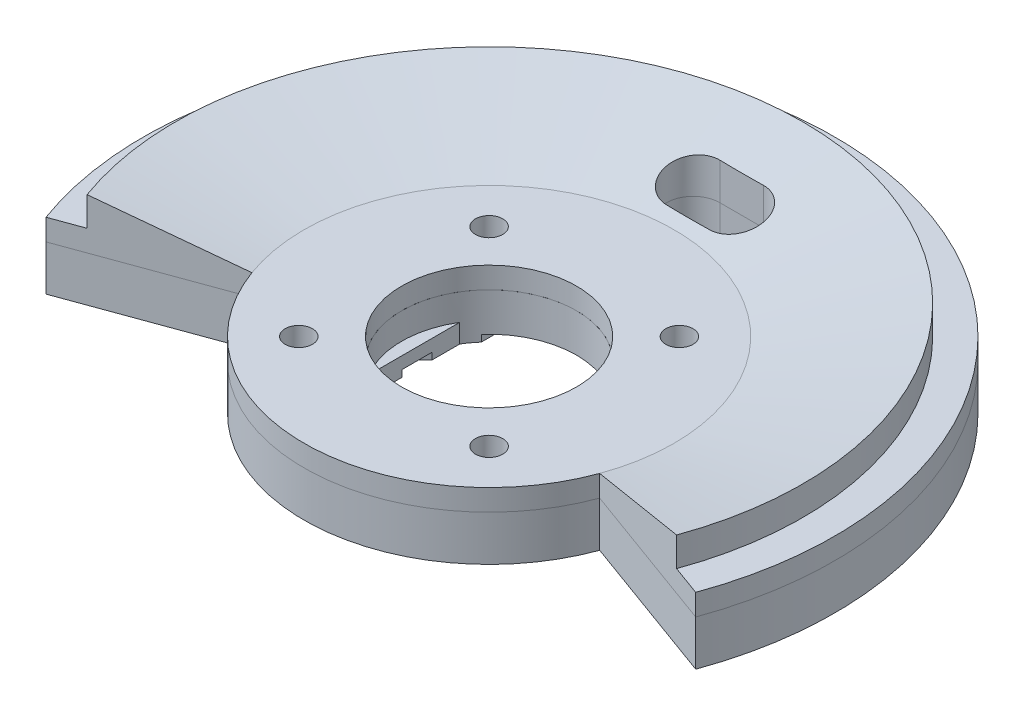
SolidWorks part; units mm, degrees
ref_plane "Front Plane" through (0, 0, 0) normal (0, 0, 1) x (1, 0, 0)
ref_plane "Top Plane" through (0, 0, 0) normal (0, 1, 0) x (1, 0, 0)
ref_plane "Right Plane" through (0, 0, 0) normal (1, 0, 0) x (0, 0, -1)
sketch "Sketch2" plane through (0, 0, 0) normal (0, 1, 0) x (1, 0, 0)
  circle A1 centre (-14.1421, 14.1421) radius 1.65 construction
  circle A2 centre (14.1421, 14.1421) radius 1.65 construction
  circle A3 centre (14.1421, -14.1421) radius 1.65 construction
  circle A4 centre (-14.1421, -14.1421) radius 1.65 construction
  circle A5 centre (0, 0) radius 13
  circle A6 centre (-14.1421, 14.1421) radius 1.65 construction
  circle A7 centre (14.1421, 14.1421) radius 1.65 construction
  circle A8 centre (14.1421, -14.1421) radius 1.65 construction
  circle A9 centre (-14.1421, -14.1421) radius 1.65 construction
  arc A10 (10.7886, -7.253) -> (10.7886, 7.253) centre (0, 0) ccw construction
  circle A11 centre (0, 0) radius 27.5
  circle A12 centre (0, 0) radius 27.5 construction
  circle A13 centre (-14.1421, -14.1421) radius 2.025
  circle A14 centre (14.1421, -14.1421) radius 2.025
  circle A15 centre (14.1421, 14.1421) radius 2.025
  circle A16 centre (-14.1421, 14.1421) radius 2.025
  dimension "D1" = 4.05
extrude "Boss-Extrude1" add sketch "Sketch2" against normal blind 3.175 from surface at -14.125
sketch "Sketch3" plane through (0, 0, 0) normal (0, 1, 0) x (1, 0, 0)
  circle A0 centre (0, 0) radius 12
  circle A1 centre (0, 0) radius 12 construction
  circle A2 centre (0, 0) radius 18.35
  dimension "D1" = 6.35
extrude "Boss-Extrude2" add sketch "Sketch3" along normal blind 6 from surface separate body
sketch "Sketch4" plane through (0, 0, 0) normal (1, 0, 0) x (0, 0, -1)
  line L0 (27.5, -17.3) -> (51.3863, -17.3)
  line L1 (51.3863, -17.3) -> (51.3863, 34.4275)
  line L2 (27.5, -14.125) -> (46.6238, -9.7953)
  line L3 (36.33, -12.1258) -> (45.83, -9.975) construction
  line L4 (45.83, -9.975) -> (45.83, 5.525) construction
  line L5 (46.6238, -9.7953) -> (46.6238, 28.4275)
  line L7 (46.6238, 28.4275) -> (18.35, 28.4275)
  line L9 (51.3863, 34.4275) -> (18.35, 34.4275)
  line L10 (18.35, 34.4275) -> (18.35, 28.4275)
  line L16 (0, -14.125) -> (0, 28.4275) construction
  line L17 (13, -14.125) -> (-13, -14.125) construction
  line L18 (-18.35, 28.4275) -> (18.35, 28.4275) construction
  line L19 (27.5, -17.3) -> (27.5, -14.125)
  dimension "D1" = 0.7937
  dimension "D2" = 4.7625
revolve "Revolve1" add sketch "Sketch4" angle 220 mid plane about L16
sketch "Sketch5" plane through (0, 28.4275, 0) normal (0, -1, 0) x (1, 0, 0)
  circle A0 centre (0, 0) radius 11.2063
  circle A1 centre (0, 0) radius 18.35
  arc A2 (17.2434, 6.2761) -> (-17.2434, 6.2761) centre (0, 0) ccw construction
  circle A3 centre (0, 0) radius 12 construction
  dimension "D1" = 0.7937
extrude "Boss-Extrude3" add sketch "Sketch5" along normal blind 0.7937
fillet "Fillet1" [suppressed] radius 1.5875
sketch "Sketch6" plane through (0, -17.3, 0) normal (0, -1, 0) x (-1, 0, 0)
  line L0 (3.25, 33.58) -> (-3.25, 33.58) construction
  line L1 (3.25, 29.6113) -> (-3.25, 29.6113)
  line L2 (3.25, 37.5488) -> (-3.25, 37.5488)
  arc A0 (3.25, 29.6113) -> (3.25, 37.5488) centre (3.25, 33.58) ccw
  arc A1 (-3.25, 37.5488) -> (-3.25, 29.6113) centre (-3.25, 33.58) ccw
  point P4 (0, 33.58)
  dimension "D1" = 7.9375
extrude "Cut-Extrude1" cut sketch "Sketch6" against normal up to next
sketch "Sketch7" plane through (0, 34.4275, 0) normal (0, 1, 0) x (1, 0, 0)
  line L0 (-48.2873, -17.5751) -> (-43.812, -15.9463)
  line L1 (43.812, -15.9463) -> (48.2873, -17.5751)
  arc A0 (48.2873, -17.5751) -> (-48.2873, -17.5751) centre (0, 0) ccw construction
  arc A1 (43.812, -15.9463) -> (-43.812, -15.9463) centre (0, 0) ccw construction
  arc A2 (48.2873, -17.5751) -> (-48.2873, -17.5751) centre (0, 0) ccw
  arc A3 (43.812, -15.9463) -> (-43.812, -15.9463) centre (0, 0) ccw
extrude "Cut-Extrude2" cut sketch "Sketch7" against normal offset from surface (48.5525 mm away) 3.175 up to face at (0, -17.3, -33.58)
sketch "Sketch8" plane through (0, -17.3, 0) normal (0, -1, 0) x (1, 0, 0)
  line L2 (-3.25, -37.5488) -> (3.25, -37.5488)
  line L3 (3.25, -29.6113) -> (-3.25, -29.6113)
  line L4 (-3.25, -37.5488) -> (3.25, -37.5488)
  line L5 (3.25, -29.6113) -> (-3.25, -29.6113)
  line L6 (-25.8415, 9.4056) -> (-48.2873, 17.5751)
  line L7 (48.2873, 17.5751) -> (25.8415, 9.4056)
  line L8 (-25.8415, 9.4056) -> (-48.2873, 17.5751)
  line L9 (48.2873, 17.5751) -> (25.8415, 9.4056)
  circle A1 centre (-14.1421, -14.1421) radius 2.025
  arc A2 (3.25, -37.5488) -> (3.25, -29.6113) centre (3.25, -33.58) ccw
  arc A3 (-3.25, -29.6113) -> (-3.25, -37.5488) centre (-3.25, -33.58) ccw
  arc A4 (3.25, -37.5488) -> (3.25, -29.6113) centre (3.25, -33.58) ccw
  arc A5 (-3.25, -29.6113) -> (-3.25, -37.5488) centre (-3.25, -33.58) ccw
  circle A6 centre (-14.1421, -14.1421) radius 2.025
  circle A7 centre (14.1421, -14.1421) radius 2.025
  circle A8 centre (14.1421, -14.1421) radius 2.025
  circle A9 centre (14.1421, 14.1421) radius 2.025
  circle A10 centre (14.1421, 14.1421) radius 2.025
  circle A11 centre (-14.1421, 14.1421) radius 2.025
  circle A12 centre (-14.1421, 14.1421) radius 2.025
  circle A13 centre (0, 0) radius 13
  circle A14 centre (0, 0) radius 13
  arc A16 (25.8415, 9.4056) -> (-25.8415, 9.4056) centre (0, 0) ccw
  arc A17 (-48.2873, 17.5751) -> (48.2873, 17.5751) centre (0, 0) ccw
  arc A18 (25.8415, 9.4056) -> (-25.8415, 9.4056) centre (0, 0) ccw
  arc A19 (-48.2873, 17.5751) -> (48.2873, 17.5751) centre (0, 0) ccw
  dimension "D1" = 0
  dimension "D2" = 0
  dimension "D3" = 0
  dimension "D4" = 0
  dimension "D5" = 0
  dimension "D6" = 0
  dimension "D7" = 0
extrude "Boss-Extrude4" add sketch "Sketch8" along normal up to surface (6.7238 mm away) separate body
sketch "Sketch10" plane through (0, -24.0238, 0) normal (0, -1, 0) x (1, 0, 0)
  line L0 (-11.1125, 0) -> (11.1125, 0) construction
  line L1 (-11.1125, 6.7463) -> (-13, 6.7463)
  line L2 (-11.1125, 6.7463) -> (-11.1125, -6.7463)
  line L3 (-11.1125, -6.7463) -> (-13, -6.7463)
  line L4 (-13, 6.7463) -> (-13, -6.7463)
  line L5 (13, 6.7463) -> (11.1125, 6.7463)
  line L6 (13, 6.7463) -> (13, -6.7463)
  line L7 (13, -6.7463) -> (11.1125, -6.7463)
  line L8 (11.1125, 6.7463) -> (11.1125, -6.7463)
  circle A0 centre (0, 0) radius 13 construction
  point P12 (0, 0)
  dimension "D1" = 22.225
ref_plane "Plane1" through (-10.7886, -14.125, -7.253) normal (-0.5579, 0, 0.8299) x (0.8299, 0, 0.5579)
ref_plane "Plane2" through (-10.7886, -14.125, -7.253) normal (-0.5579, 0, 0.8299) x (0.8299, 0, 0.5579)
extrude "Boss-Extrude5" add sketch "Sketch10" against normal offset from surface (2.7938 mm away) 1.5875
sketch "Sketch12" plane through (0, -24.0238, 0) normal (0, -1, 0) x (1, 0, 0)
  line L0 (-9.754, -3.9818) -> (-9.754, -20.6306)
  line L1 (-9.754, -20.6306) -> (9.754, -20.6306)
  line L6 (9.754, -20.6306) -> (9.754, -3.9818)
  line L7 (9.754, -3.9818) -> (12.754, -0.9818)
  line L8 (12.754, -0.9818) -> (12.754, 0.2286)
  line L9 (12.754, 0.2286) -> (9.754, 3.2286)
  line L10 (9.754, 3.2286) -> (9.754, 4.8774)
  line L11 (9.754, 4.8774) -> (-9.754, 4.8774)
  line L12 (-9.754, 4.8774) -> (-9.754, 3.2286)
  line L13 (-9.754, 3.2286) -> (-12.754, 0.2286)
  line L14 (-12.754, 0.2286) -> (-12.754, -0.9818)
  line L15 (-12.754, -0.9818) -> (-9.754, -3.9818)
  line L16 (-9.5, -3.8766) -> (-9.5, -20.3766)
  line L17 (-9.5, -20.3766) -> (9.5, -20.3766)
  line L18 (9.5, -20.3766) -> (9.5, -3.8766)
  line L19 (9.5, -3.8766) -> (12.5, -0.8766)
  line L20 (12.5, -0.8766) -> (12.5, 0.1234)
  line L21 (12.5, 0.1234) -> (9.5, 3.1234)
  line L22 (9.5, 3.1234) -> (9.5, 4.6234)
  line L23 (9.5, 4.6234) -> (-9.5, 4.6234)
  line L24 (-9.5, 4.6234) -> (-9.5, 3.1234)
  line L25 (-9.5, 3.1234) -> (-12.5, 0.1234)
  line L26 (-12.5, 0.1234) -> (-12.5, -0.8766)
  line L27 (-12.5, -0.8766) -> (-9.5, -3.8766)
  line L28 (-9.5, -3.8766) -> (-9.5, -20.3766) construction
  line L29 (-9.5, -20.3766) -> (9.5, -20.3766) construction
  line L30 (9.5, -20.3766) -> (9.5, -3.8766) construction
  line L31 (9.5, -3.8766) -> (12.5, -0.8766) construction
  line L32 (12.5, -0.8766) -> (12.5, 0.1234) construction
  line L33 (12.5, 0.1234) -> (9.5, 3.1234) construction
  line L34 (9.5, 3.1234) -> (9.5, 4.6234) construction
  line L35 (9.5, 4.6234) -> (-9.5, 4.6234) construction
  line L36 (-9.5, 4.6234) -> (-9.5, 3.1234) construction
  line L37 (-9.5, 3.1234) -> (-12.5, 0.1234) construction
  line L38 (-12.5, 0.1234) -> (-12.5, -0.8766) construction
  line L39 (-12.5, -0.8766) -> (-9.5, -3.8766) construction
  dimension "D2" = 0
  dimension "D3" = 0.254
extrude "Cut-Extrude3" cut sketch "Sketch12" against normal up to surface (1 mm away)
